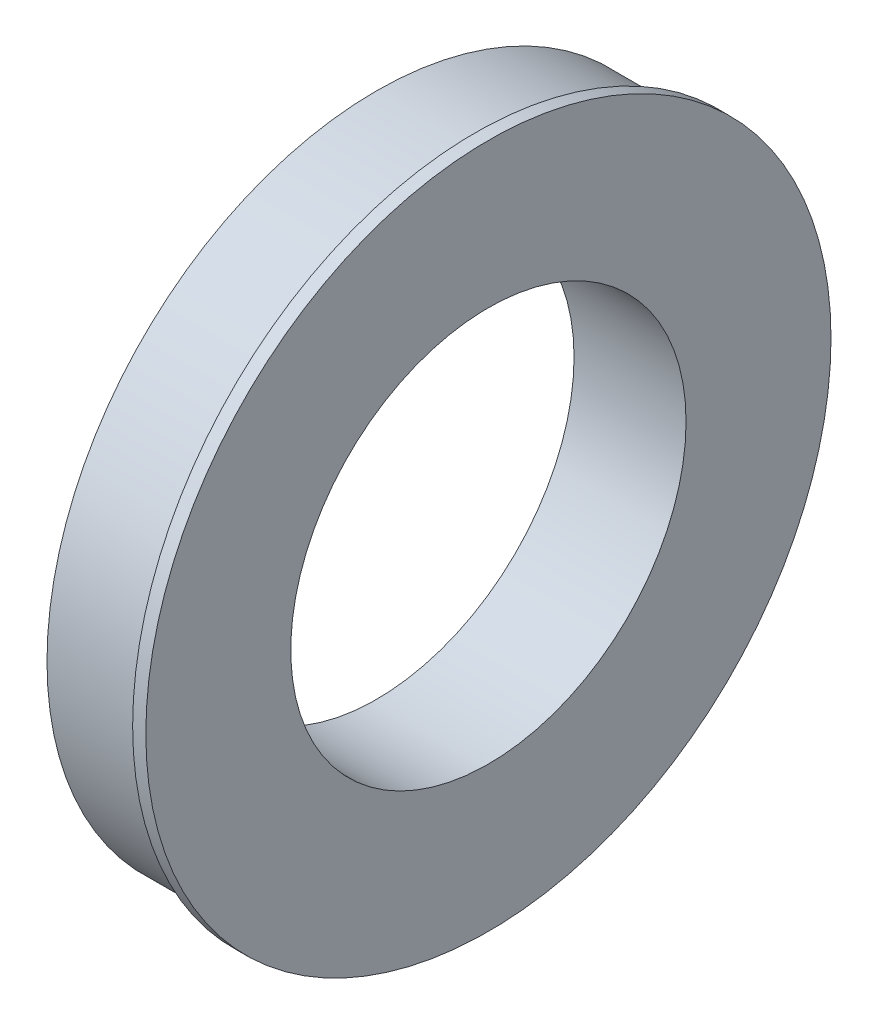
SolidWorks part; units mm, degrees
ref_plane "Front Plane" through (0, 0, 0) normal (0, 0, 1) x (1, 0, 0)
ref_plane "Top Plane" through (0, 0, 0) normal (0, 1, 0) x (1, 0, 0)
ref_plane "Right Plane" through (0, 0, 0) normal (1, 0, 0) x (0, 0, -1)
sketch "Sketch2" plane through (0, 0, 0) normal (1, 0, 0) x (0, 0, -1)
  circle A0 centre (0, 0) radius 38.1
  circle A1 centre (0, 0) radius 63.5
  dimension "D1" = 76.2
  dimension "D2" = 127
extrude "Boss-Extrude1" add sketch "Sketch2" along normal blind 19.05
sketch "Sketch3" plane through (19.05, 0, 0) normal (1, 0, 0) x (0, 0, -1)
  circle A0 centre (0, 0) radius 38.1 construction
  circle A1 centre (0, 0) radius 38.1
  circle A2 centre (0, 0) radius 66.04
  dimension "D1" = 132.08
extrude "Boss-Extrude2" add sketch "Sketch3" along normal blind 2.54
